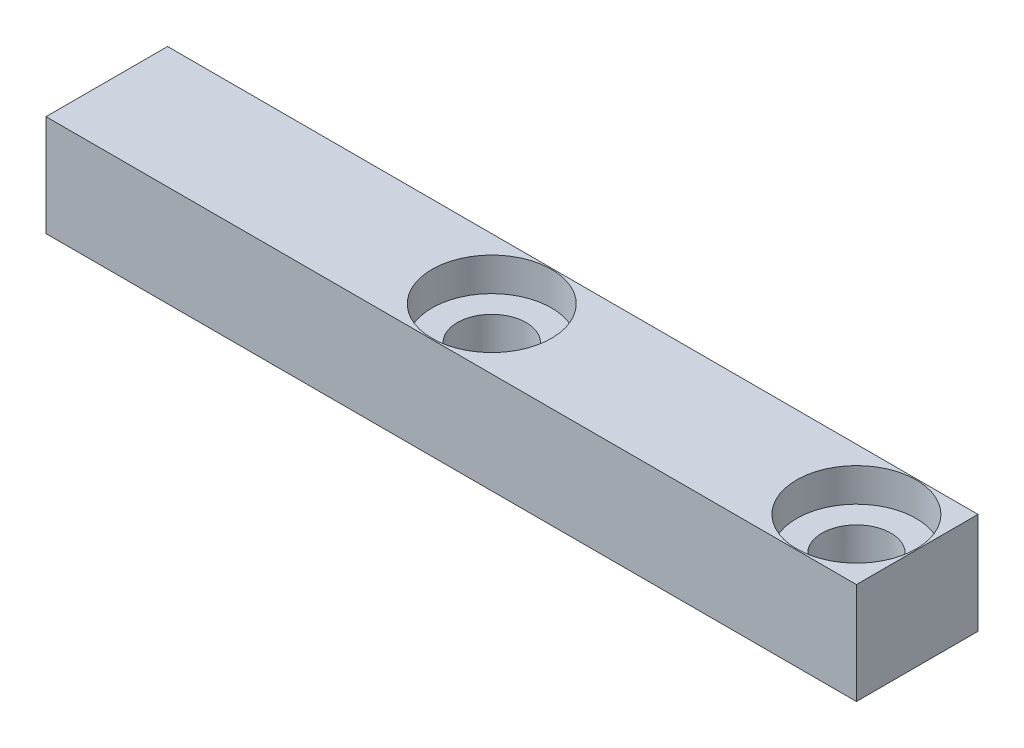
SolidWorks part; units mm, degrees
ref_plane "Front Plane" through (0, 0, 0) normal (0, 0, 1) x (1, 0, 0)
ref_plane "Top Plane" through (0, 0, 0) normal (0, 1, 0) x (1, 0, 0)
ref_plane "Right Plane" through (0, 0, 0) normal (1, 0, 0) x (0, 0, -1)
sketch "Sketch1" plane through (0, 0, 0) normal (0, 1, 0) x (1, 0, 0)
  line L1 (0, 0) -> (40, 0)
  line L2 (0, 0) -> (0, 6)
  line L3 (0, 6) -> (40, 6)
  line L4 (40, 0) -> (40, 6)
  dimension "D1" = 6
  dimension "D2" = 40
extrude "Boss-Extrude1" add sketch "Sketch1" along normal blind 5
hole_wizard "CBORE for M3 SBHCS1" positions "Sketch2" profile "Sketch3" counterbore size "M3" standard "ANSI Metric"
sketch "Sketch2" plane through (0, 5, 0) normal (0, 1, 0) x (1, 0, 0)
  line L0 (40, 0) -> (40, 6) construction
  line L1 (0, 0) -> (40, 0) construction
  point P0 (37, 3)
  point P2 (19, 3)
  dimension "D1" = 18
  dimension "D2" = 3
  dimension "D3" = 3
sketch "Sketch3" plane through (37, 5, -3) normal (1, 0, 0) x (0, 0, 1)
  line L0 (0, 0) -> (0, 8.5215)
  line L1 (0, 8.5215) -> (1.7, 7.5)
  line L2 (1.7, 7.5) -> (1.7, 1.65)
  line L3 (1.7, 1.65) -> (2.95, 1.65)
  line L4 (2.95, 1.65) -> (2.95, 0)
  line L5 (2.95, 0) -> (0, 0)
  line L10 (0, 8.5215) -> (-1.7, 7.5) construction
  line L11 (0, -6.35) -> (0, 107.95) construction
  dimension "Hole Dia." = 3.4
  dimension "Hole Depth" = 7.5
  dimension "C'Bore Dia." = 5.9
  dimension "C'Bore Depth" = 1.65
  dimension "Drill Angle" = 118
